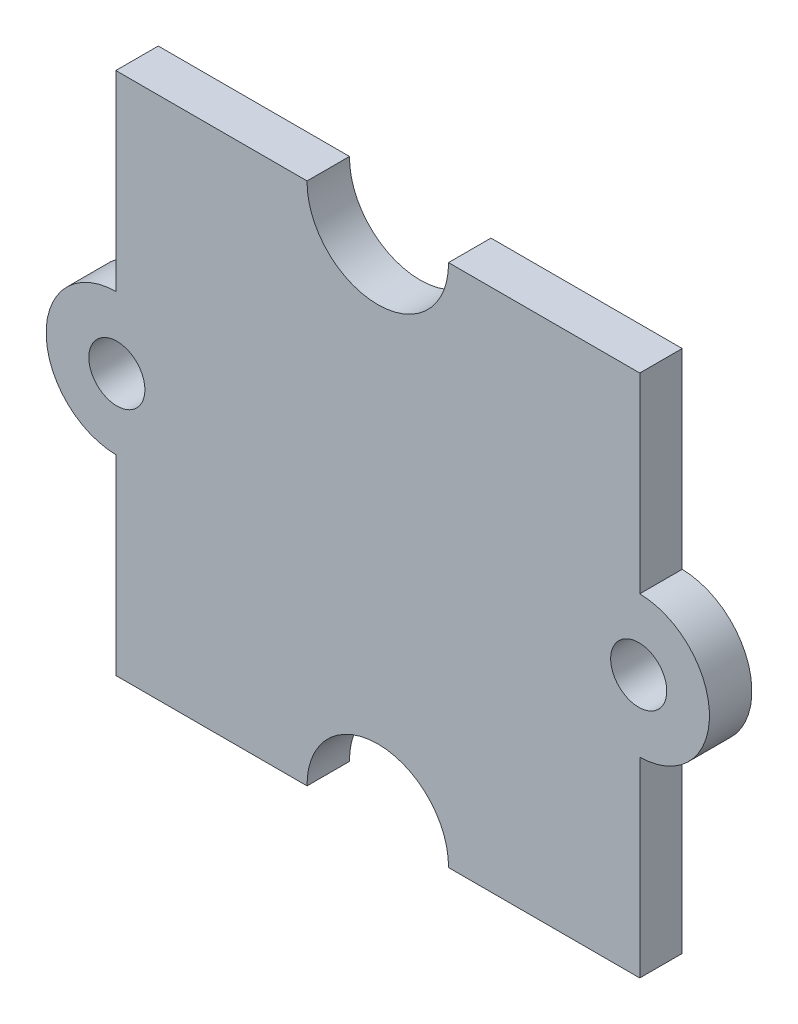
SolidWorks part; units mm, degrees
ref_plane "Plan de face" through (0, 0, 0) normal (0, 0, 1) x (1, 0, 0)
ref_plane "Plan de dessus" through (0, 0, 0) normal (0, 1, 0) x (1, 0, 0)
ref_plane "Plan de droite" through (0, 0, 0) normal (1, 0, 0) x (0, 0, -1)
sketch "Esquisse1" plane through (0, 0, 0) normal (0, 0, 1) x (1, 0, 0)
  line L0 (0, 13.7908) -> (0, -14.5752) construction
  line L1 (-18.6928, 0) -> (16.3399, 0) construction
  line L2 (-10, -2.6997) -> (-10, -10)
  line L3 (-10, 10) -> (-2.6997, 10)
  line L4 (-10, 10) -> (-10, 2.6997)
  line L5 (-10, -10) -> (-2.6997, -10)
  line L6 (10, 10) -> (10, 2.6997)
  line L7 (10, -2.6997) -> (10, -10)
  line L8 (2.6997, 10) -> (10, 10)
  line L9 (2.6997, -10) -> (10, -10)
  circle A0 centre (-9.96, 0) radius 1.07
  circle A1 centre (9.96, 0) radius 1.07
  arc A2 (-10, 2.6997) -> (-10, -2.6997) centre (-9.96, 0) ccw
  arc A3 (10, -2.6997) -> (10, 2.6997) centre (9.96, 0) ccw
  arc A4 (-2.6997, 10) -> (2.6997, 10) centre (0, 9.96) ccw
  arc A5 (2.6997, -10) -> (-2.6997, -10) centre (0, -9.96) ccw
  dimension "D4" = 2.14
  dimension "D5" = 2.14
  dimension "D6" = 2.7
  dimension "D7" = 2.7
  dimension "D9" = 5.4
  dimension "D10" = 5.4
  dimension "D1" = 20
  dimension "D2" = 20
  dimension "D3" = 19.92
  dimension "D8" = 19.92
extrude "Boss.-Extru.1" add sketch "Esquisse1" along normal blind 1.62
